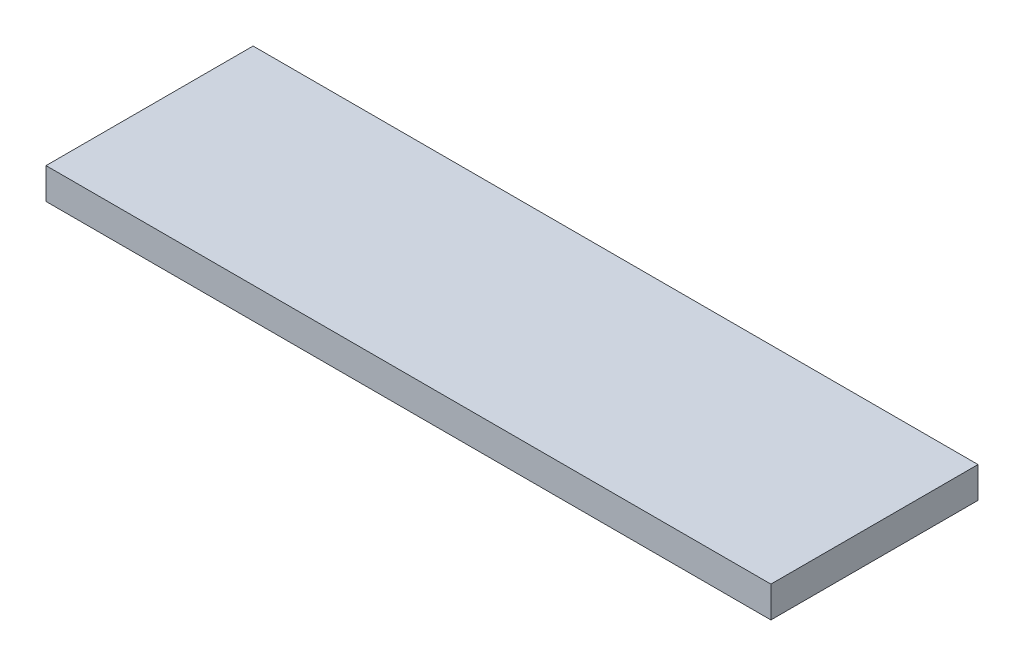
SolidWorks part; units mm, degrees
ref_plane "Спереди" through (0, 0, 0) normal (0, 0, 1) x (1, 0, 0)
ref_plane "Сверху" through (0, 0, 0) normal (0, 1, 0) x (1, 0, 0)
ref_plane "Справа" through (0, 0, 0) normal (1, 0, 0) x (0, 0, -1)
other "Configuration Table"
sketch "Эскиз1" plane through (0, 0, 0) normal (0, 1, 0) x (1, 0, 0)
  line L1 (0, 0) -> (70, 0)
  line L2 (0, 0) -> (0, 20)
  line L3 (0, 20) -> (70, 20)
  line L4 (70, 0) -> (70, 20)
  dimension "D1" = 20
  dimension "D2" = 70
extrude "Бобышка-Вытянуть1" add sketch "Эскиз1" along normal blind 3
